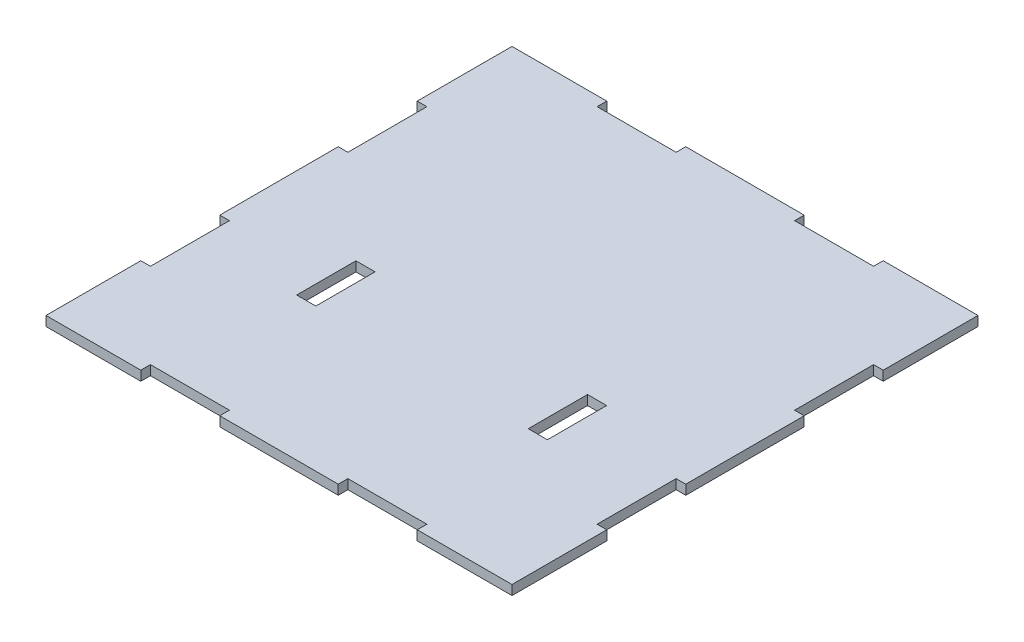
SolidWorks part; units mm, degrees
ref_plane "Alzado" through (0, 0, 0) normal (0, 0, 1) x (1, 0, 0)
ref_plane "Planta" through (0, 0, 0) normal (0, 1, 0) x (1, 0, 0)
ref_plane "Vista lateral" through (0, 0, 0) normal (1, 0, 0) x (0, 0, -1)
sketch "Croquis1" plane through (0, 0, 0) normal (0, 1, 0) x (1, 0, 0)
  line L0 (0, 0) -> (0, -59) construction
  line L1 (-59, -59) -> (-35, -59)
  line L2 (-59, -59) -> (-59, -35)
  line L3 (-59, 59) -> (-35, 59)
  line L4 (59, -59) -> (59, -35)
  line L5 (-59, -59) -> (59, 59) construction
  line L6 (-59, 59) -> (59, -59) construction
  line L7 (-31.74, -7.78) -> (-26.9, -7.78)
  line L8 (-31.74, -7.78) -> (-31.74, -22.78)
  line L9 (-31.74, -22.78) -> (-26.9, -22.78)
  line L10 (-26.9, -7.78) -> (-26.9, -22.78)
  line L11 (-31.74, -7.78) -> (-26.9, -22.78) construction
  line L12 (-31.74, -22.78) -> (-26.9, -7.78) construction
  line L13 (31.74, -22.78) -> (26.9, -7.78) construction
  line L14 (31.74, -7.78) -> (26.9, -22.78) construction
  line L15 (26.9, -7.78) -> (26.9, -22.78)
  line L16 (31.74, -22.78) -> (26.9, -22.78)
  line L17 (31.74, -7.78) -> (31.74, -22.78)
  line L18 (31.74, -7.78) -> (26.9, -7.78)
  line L19 (0, 0) -> (-59, 0) construction
  line L20 (-15, 59) -> (15, 59)
  line L21 (-15, 56.56) -> (-35, 56.56)
  line L22 (-15, 56.56) -> (-15, 59)
  line L23 (15, 56.56) -> (15, 59)
  line L24 (-35, 56.56) -> (-35, 59)
  line L25 (-15, 56.56) -> (-35, 59) construction
  line L26 (-15, 59) -> (-35, 56.56) construction
  line L27 (15, 56.56) -> (35, 56.56)
  line L28 (35, 56.56) -> (35, 59)
  line L29 (35, 59) -> (59, 59)
  line L30 (-15, -56.56) -> (-15, -59)
  line L31 (-15, -56.56) -> (-35, -56.56)
  line L32 (-35, -56.56) -> (-35, -59)
  line L33 (35, -56.56) -> (35, -59)
  line L34 (15, -56.56) -> (35, -56.56)
  line L35 (15, -56.56) -> (15, -59)
  line L36 (-15, -59) -> (15, -59)
  line L37 (35, -59) -> (59, -59)
  line L38 (-59, 35) -> (-59, 59)
  line L39 (-56.56, 35) -> (-59, 35)
  line L40 (-56.56, 35) -> (-56.56, 15)
  line L41 (-56.56, 15) -> (-59, 15)
  line L42 (-56.56, -35) -> (-59, -35)
  line L43 (-56.56, 35) -> (-59, 15) construction
  line L44 (-56.56, 15) -> (-59, 35) construction
  line L45 (-56.56, -15) -> (-59, -15)
  line L46 (-56.56, -35) -> (-56.56, -15)
  line L47 (-59, -15) -> (-59, 15)
  line L48 (56.56, -35) -> (59, -35)
  line L49 (56.56, -35) -> (56.56, -15)
  line L50 (56.56, -15) -> (59, -15)
  line L51 (56.56, 35) -> (59, 35)
  line L52 (56.56, 15) -> (59, 15)
  line L53 (56.56, 35) -> (56.56, 15)
  line L54 (59, 35) -> (59, 59)
  line L55 (59, -15) -> (59, 15)
  point P0 (0, 0)
  point P6 (-29.32, -15.28)
  point P17 (29.32, -15.28)
  point P19 (-25, 57.78)
  point P36 (-57.78, 25)
  dimension "D1" = 118
  dimension "D2" = 118
  dimension "D3" = 36.22
  dimension "D4" = 27.26
  dimension "D5" = 15
  dimension "D6" = 4.84
  dimension "D7" = 15
  dimension "D8" = 20
  dimension "D9" = 2.44
  dimension "D10" = 15
  dimension "D11" = 20
  dimension "D12" = 2.44
extrude "Saliente-Extruir1" add sketch "Croquis1" along normal blind 2.44
